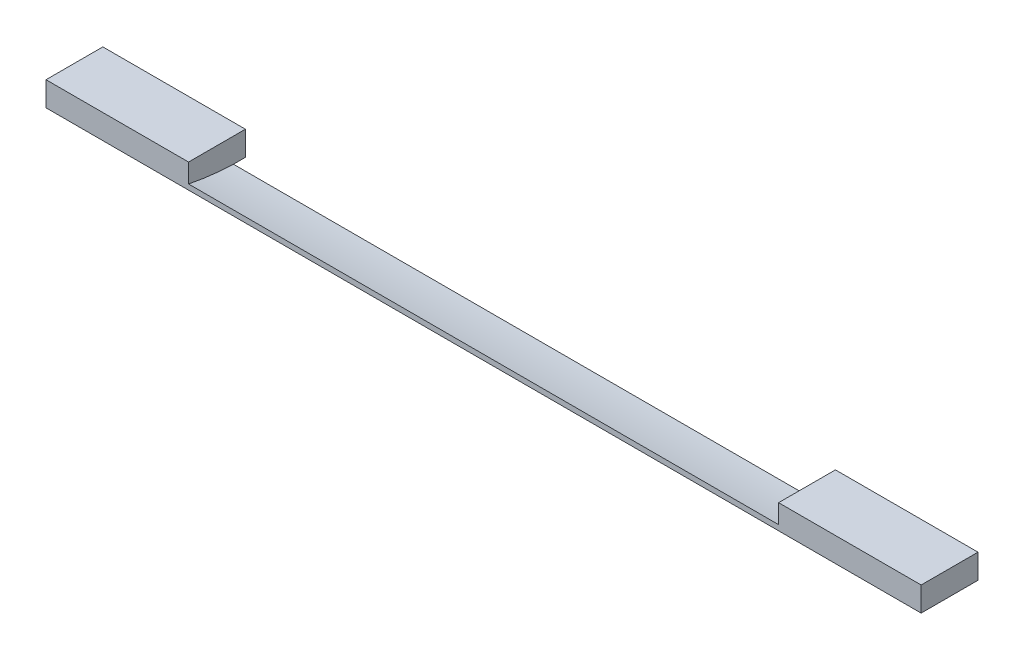
SolidWorks part; units mm, degrees
material "Pine"
ref_plane "Front Plane" through (0, 0, 0) normal (0, 0, 1) x (1, 0, 0)
ref_plane "Top Plane" through (0, 0, 0) normal (0, 1, 0) x (1, 0, 0)
ref_plane "Right Plane" through (0, 0, 0) normal (1, 0, 0) x (0, 0, -1)
sketch "Sketch1" plane through (0, 0, 0) normal (0, 1, 0) x (1, 0, 0)
  line L0 (0, 0) -> (0, 163.4625) construction
  line L1 (-684.2125, 0) -> (684.2125, 0)
  line L2 (-684.2125, 0) -> (-684.2125, 88.9)
  line L3 (-684.2125, 88.9) -> (684.2125, 88.9)
  line L4 (684.2125, 0) -> (684.2125, 88.9)
  dimension "D1" = 88.9
  dimension "D2" = 1368.425
extrude "Boss-Extrude1" add sketch "Sketch1" along normal blind 38.1
sketch "Sketch3" plane through (0, 0, 0) normal (-1, 0, 0) x (0, 0, 1)
  line L4 (-73.5013, 433.324) -> (-98.7107, 433.324) construction
  line L7 (-86.106, 457.0857) -> (-86.106, 409.5623) construction
  line L12 (-88.9, 0) -> (0, 0)
  line L13 (0, 0) -> (0, 38.1)
  line L14 (0, 38.1) -> (-88.9, 38.1)
  line L15 (-88.9, 38.1) -> (-88.9, 0)
  line L16 (-88.9, 0) -> (-70.1927, 0)
  line L17 (0, 8.3432) -> (0, 38.1)
  line L18 (0, 38.1) -> (-88.9, 38.1)
  line L19 (-88.9, 38.1) -> (-88.9, 0)
  arc A0 (-70.1927, 0) -> (0, 8.3432) centre (-86.106, 433.324) ccw
  point P4 (-86.106, 433.324)
  point P5 (0, 0)
  point P6 (0, 0)
  dimension "D2" = 0
  dimension "D1" = 433.6161
  dimension "D3" = 86.106
  dimension "D5" = 433.324
extrude "Cut-Extrude2" cut sketch "Sketch3" against normal mid plane 922.6042
